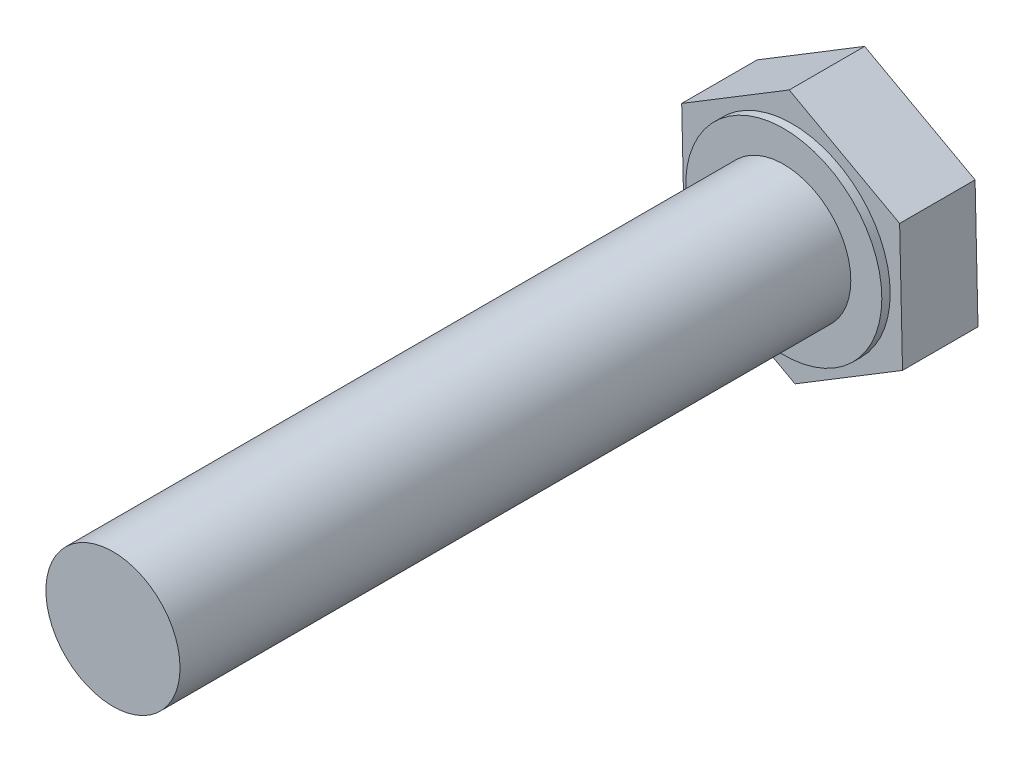
SolidWorks part; units mm, degrees
ref_plane "Front Plane" through (0, 0, 0) normal (0, 0, 1) x (1, 0, 0)
ref_plane "Top Plane" through (0, 0, 0) normal (0, 1, 0) x (1, 0, 0)
ref_plane "Right Plane" through (0, 0, 0) normal (1, 0, 0) x (0, 0, -1)
sketch "Sketch1" plane through (0, 0, 0) normal (0, 0, 1) x (1, 0, 0)
  line L1 (-6.4115, -3.902) -> (0.1734, -7.5035)
  line L2 (0.1734, -7.5035) -> (6.585, -3.6016)
  line L3 (6.585, -3.6016) -> (6.4115, 3.902)
  line L4 (6.4115, 3.902) -> (-0.1734, 7.5035)
  line L5 (-0.1734, 7.5035) -> (-6.585, 3.6016)
  line L6 (-6.585, 3.6016) -> (-6.4115, -3.902)
  circle A0 centre (0, 0) radius 6.5 construction
  dimension "D1" = 13
extrude "Boss-Extrude1" add sketch "Sketch1" along normal blind 4.5
sketch "Sketch2" plane through (0, 0, 4.5) normal (0, 0, 1) x (1, 0, 0)
  circle A0 centre (0, 0) radius 5.85
  dimension "D1" = 11.7
extrude "Boss-Extrude2" add sketch "Sketch2" along normal blind 0.5
sketch "Sketch3" plane through (0, 0, 5) normal (0, 0, 1) x (1, 0, 0)
  circle A0 centre (0, 0) radius 4
  dimension "D1" = 8
extrude "Boss-Extrude3" add sketch "Sketch3" along normal blind 40
